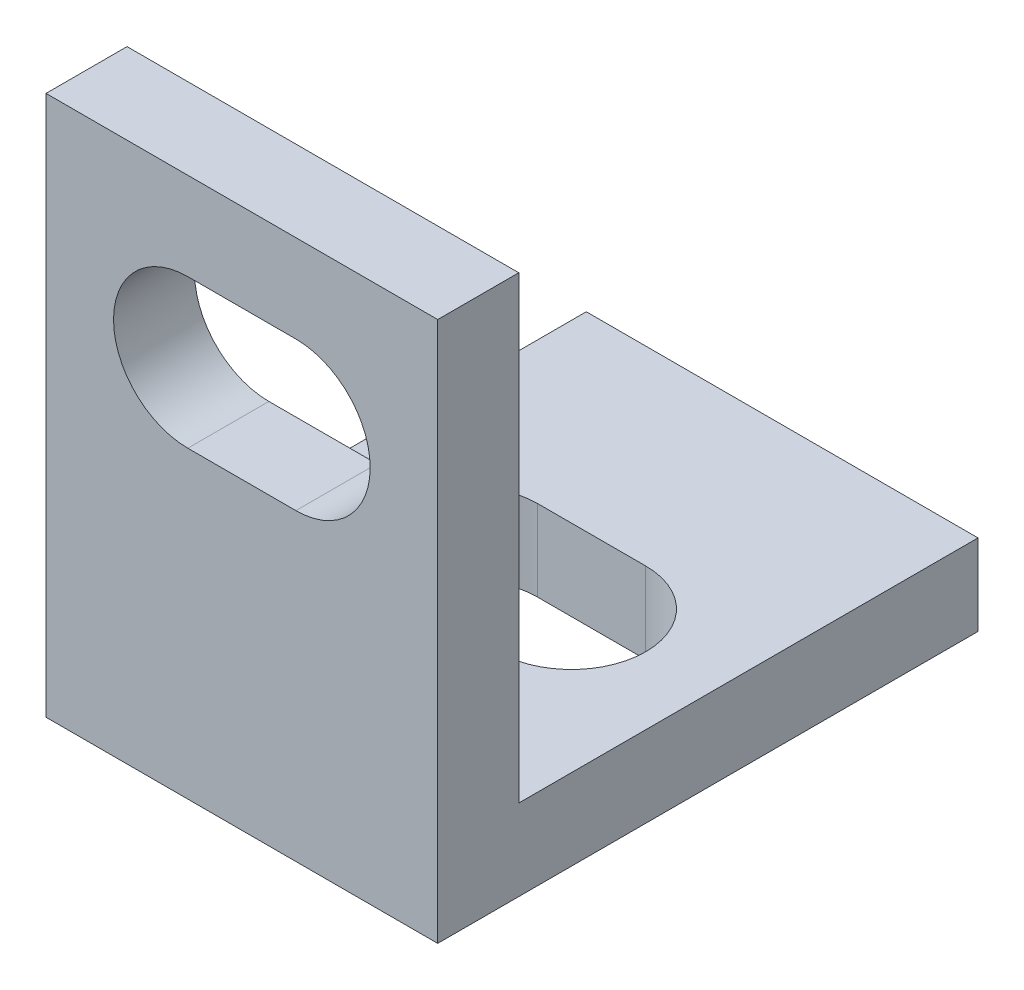
SolidWorks part; units mm, degrees
ref_plane "Front Plane" through (0, 0, 0) normal (0, 0, 1) x (1, 0, 0)
ref_plane "Top Plane" through (0, 0, 0) normal (0, 1, 0) x (1, 0, 0)
ref_plane "Right Plane" through (0, 0, 0) normal (1, 0, 0) x (0, 0, -1)
sketch "Sketch1" plane through (0, 0, 0) normal (1, 0, 0) x (0, 0, -1)
  line L0 (0, 0) -> (0, 20)
  line L1 (0, 20) -> (3, 20)
  line L2 (3, 20) -> (3, 3)
  line L3 (3, 3) -> (20, 3)
  line L4 (20, 3) -> (20, 0)
  line L5 (20, 0) -> (0, 0)
  dimension "D1" = 20
  dimension "D2" = 3
extrude "Boss-Extrude1" add sketch "Sketch1" along normal blind 14.5
sketch "Sketch2" plane through (0, 0, 0) normal (0, 0, 1) x (1, 0, 0)
  line L0 (5.25, 14) -> (9.25, 14) construction
  line L1 (5.25, 16.75) -> (9.25, 16.75)
  line L2 (5.25, 11.25) -> (9.25, 11.25)
  line L3 (7.25, 14) -> (7.25, 20) construction
  line L4 (14.5, 20) -> (0, 20) construction
  arc A0 (5.25, 16.75) -> (5.25, 11.25) centre (5.25, 14) ccw
  arc A1 (9.25, 11.25) -> (9.25, 16.75) centre (9.25, 14) ccw
  point P2 (7.25, 14)
  dimension "D2" = 2.75
  dimension "D1" = 4
  dimension "D3" = 3.25
extrude "Cut-Extrude1" cut sketch "Sketch2" against normal through all contours A1 L1 A0 L2
sketch "Sketch3" plane through (0, 0, 0) normal (0, -1, 0) x (1, 0, 0)
  line L0 (5.25, -10.2) -> (9.25, -10.2) construction
  line L1 (5.25, -7.45) -> (9.25, -7.45)
  line L2 (5.25, -12.95) -> (9.25, -12.95)
  line L3 (14.5, 0) -> (0, 0) construction
  line L4 (7.25, -10.2) -> (7.25, -20) construction
  line L5 (14.5, -20) -> (0, -20) construction
  arc A0 (5.25, -7.45) -> (5.25, -12.95) centre (5.25, -10.2) ccw
  arc A1 (9.25, -12.95) -> (9.25, -7.45) centre (9.25, -10.2) ccw
  point P2 (7.25, -10.2)
  dimension "D1" = 2.75
  dimension "D2" = 4
  dimension "D3" = 7.45
extrude "Cut-Extrude2" cut sketch "Sketch3" against normal through all
equation "\"D2@Sketch2\"=5.5/2"
equation "\"D1@Sketch3\"=5.5/2"
